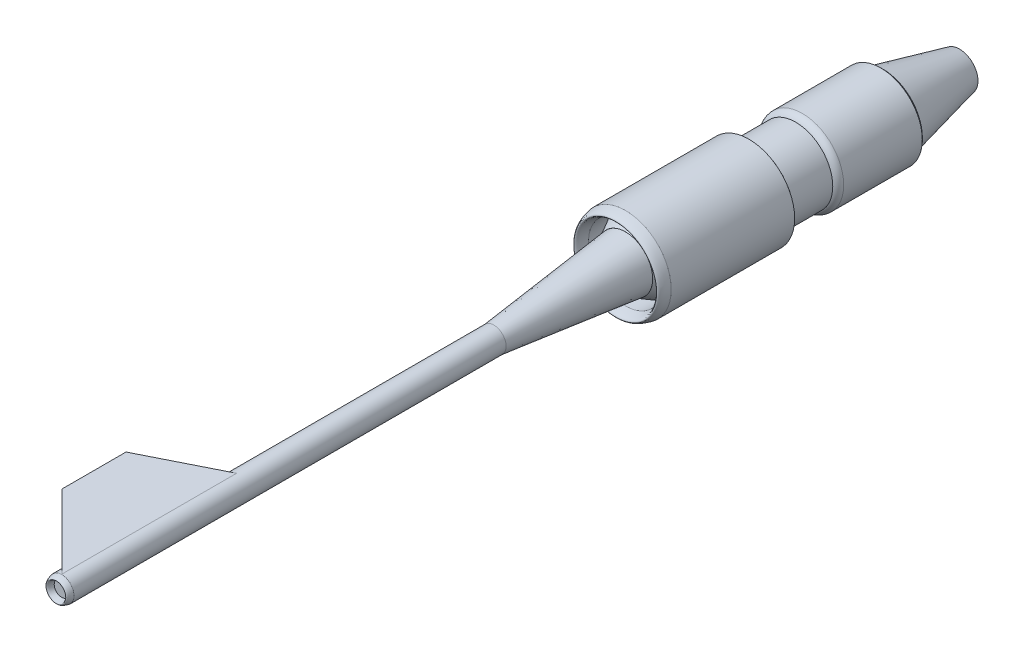
SolidWorks part; units mm, degrees
ref_plane "Front Plane" through (0, 0, 0) normal (0, 0, 1) x (1, 0, 0)
ref_plane "Top Plane" through (0, 0, 0) normal (0, 1, 0) x (1, 0, 0)
ref_plane "Right Plane" through (0, 0, 0) normal (1, 0, 0) x (0, 0, -1)
sketch "Sketch1" plane through (0, 0, 0) normal (0, 0, 1) x (1, 0, 0)
  circle A0 centre (0, 0) radius 416.25
  circle A1 centre (0, 0) radius 337.5
extrude "Boss-Extrude1" add sketch "Sketch1" against normal blind 1125
sketch "Sketch2" plane through (0, 0, 0) normal (1, 0, 0) x (0, 0, -1)
  line L0 (0, 416.25) -> (0, 337.5) construction
  line L1 (0, 337.5) -> (0, 376.875) construction
  line L2 (0, 376.875) -> (-90, 376.875) construction
  line L3 (0, 416.25) -> (0, 337.5)
  line L4 (0, 0) -> (98.8797, 0) construction
  spline S0 degree 2 poles (0, 337.5) (-180, 376.875) (0, 416.25) knots 0 0 0 1 1 1
revolve "Revolve1" add sketch "Sketch2" angle 360 about L4
ref_plane "Plane1" through (0, 0, 0) normal (0, 0, 1) x (1, 0, 0)
sketch "Sketch3" plane through (0, 0, 0) normal (0, 0, 1) x (1, 0, 0)
  circle A0 centre (0, 0) radius 247.5
sketch "Sketch4" plane through (0, 0, 0) normal (0, 1, 0) x (1, 0, 0)
  line L0 (0, 0) -> (0, -1200)
  line L1 (0, -1200) -> (112.5, -1200)
  line L2 (0, 0) -> (247.5, 0)
  line L3 (-247.5, 0) -> (247.5, 0) construction
  line L4 (-457.875, 0) -> (457.875, 0) construction
  line L5 (247.5, 0) -> (112.5, -1200)
revolve "Revolve2" add sketch "Sketch4" angle 360 about L0
sketch "Sketch5" plane through (0, 0, 1200) normal (0, 0, 1) x (1, 0, 0)
  circle A0 centre (0, 0) radius 112.5
extrude "Boss-Extrude2" add sketch "Sketch5" along normal blind 3937.5
sketch "Sketch14" plane through (0, 0, 0) normal (1, 0, 0) x (0, 0, -1)
  line L0 (-5137.5, 112.5) -> (-5137.5, 67.5)
  line L1 (-5137.5, 112.5) -> (-5137.5, -112.5) construction
  line L2 (-5137.5, 67.5) -> (-5137.5, 90)
  line L3 (-5137.5, 90) -> (-5187.5, 90) construction
  line L4 (-5137.5, 0) -> (-5198.2274, 0) construction
  line L5 (-5137.5, 112.5) -> (-5137.5, -112.5) construction
  spline S0 degree 2 poles (-5137.5, 67.5) (-5237.5, 90) (-5137.5, 112.5) knots 0 0 0 1 1 1
  dimension "D1" = 50
  dimension "D2" = 67.5
  dimension "D3" = 90
revolve "Revolve4" add sketch "Sketch14" angle 360 about L4
sketch "Sketch15" plane through (0, 0, -1125) normal (0, 0, -1) x (-1, 0, 0)
  circle A0 centre (0, 0) radius 337.5
extrude "Boss-Extrude5" add sketch "Sketch15" along normal blind 486 separate body
sketch "Sketch16" plane through (0, 0, -1611) normal (0, 0, -1) x (-1, 0, 0)
  line L0 (0, 337.5) -> (0, 416.25) construction
  line L1 (0, 376.875) -> (79.8334, 376.875) construction
  circle A0 centre (0, 0) radius 337.5 construction
  circle A1 centre (0, 0) radius 337.5 construction
  circle A2 centre (0, 0) radius 416.25 construction
  circle A4 centre (0, 0) radius 376.875
extrude "Boss-Extrude6" add sketch "Sketch16" along normal blind 716
sketch "Sketch17" plane through (0, 0, 0) normal (1, 0, 0) x (0, 0, -1)
  line L0 (2327, 0) -> (3043, 0)
  line L1 (2327, -376.875) -> (2327, 376.875) construction
  line L2 (3043, 0) -> (3043, 168.75)
  line L3 (1611, 337.5) -> (2327, 337.5) construction
  line L4 (2327, 0) -> (2327, 337.5)
  line L5 (2327, 337.5) -> (3043, 168.75)
revolve "Revolve5" add sketch "Sketch17" angle 360 about L0
sketch "Sketch18" plane through (0, 0, 0) normal (1, 0, 0) x (0, 0, -1)
  line L0 (0, 247.5) -> (306.6324, 416.25)
  line L1 (1125, 416.25) -> (0, 416.25) construction
  line L2 (0, 247.5) -> (306.6324, 247.5)
  line L3 (306.6324, 247.5) -> (306.6324, 416.25)
  line L4 (0, 0) -> (306.6324, 0) construction
revolve "Revolve6" add sketch "Sketch18" angle 360 about L4
sketch "Sketch19" plane through (0, 0, 0) normal (1, 0, 0) x (0, 0, -1)
  line L1 (1611, 337.5) -> (1611, -337.5) construction
  line L2 (1611, 0) -> (1611, 337.5) construction
  line L3 (1611, 337.5) -> (1551, 337.5)
  line L4 (1611, 0) -> (1571, 0) construction
  line L5 (1611, 337.5) -> (1125, 337.5) construction
  line L6 (1611, 337.5) -> (1611, 376.875)
  line L7 (1611, 376.875) -> (1611, -376.875) construction
  arc A0 (1551, 337.5) -> (1611, 376.875) centre (1614.9642, 305.4325) cw
revolve "Revolve9" add sketch "Sketch19" angle 360 about L4
sketch "Sketch20" plane through (0, 0, 0) normal (1, 0, 0) x (0, 0, -1)
  line L0 (1125, 337.5) -> (1125, 416.25)
  line L1 (1125, 337.5) -> (1155, 337.5)
  line L2 (1551, 337.5) -> (1125, 337.5) construction
  line L3 (1125, 0) -> (1175, 0) construction
  line L4 (1125, -416.25) -> (1125, 416.25) construction
  conic Q0 (1155, 337.5) -> (1125, 416.25) control (1155, 382.5893) rho 0.44632
revolve "Revolve11" add sketch "Sketch20" angle 360 about L3
sketch "Sketch21" plane through (0, 0, 0) normal (1, 0, 0) x (0, 0, -1)
  line L0 (2327, 337.5) -> (2327, 376.875)
  line L1 (2327, 0) -> (2377, 0) construction
  line L2 (2327, -376.875) -> (2327, 376.875) construction
  line L3 (2327, 337.5) -> (2356.2, 330.618)
  line L4 (3043, 168.75) -> (2327, 337.5) construction
  conic Q0 (2327, 376.875) -> (2356.2, 330.618) control (2356.2, 357.1875) rho 0.453502
revolve "Revolve12" add sketch "Sketch21" angle 360 about L1
sketch3d "3DSketch1"
  line L0 (1.7689, 112.4861, 5137.5) -> (-673.2311, 112.4861, 5137.5) construction
  circle A0 centre (0, 0, 5137.5) radius 112.5 construction
  point P2 (0, 0, 5250)
ref_plane "Plane2" through (0, 112.4861, 0) normal (0, 1, 0) x (1, 0, 0)
sketch "Sketch22" plane through (0, 112.4861, 0) normal (0, 1, 0) x (1, 0, 0)
  line L0 (1.7689, -5137.5) -> (1.7689, -3540)
  line L1 (-673.2311, -5137.5) -> (-673.2311, -4462.5) construction
  line L2 (-673.2311, -4462.5) -> (1.7689, -4462.5) construction
  line L3 (-673.2311, -4462.5) -> (1.7689, -5137.5)
  line L4 (-673.2311, -4462.5) -> (-673.2311, -3877.5)
  line L5 (-673.2311, -3877.5) -> (1.7689, -3540)
extrude "Boss-Extrude7" add sketch "Sketch22" against normal blind 50
sketch3d "3DSketch3"
  line L0 (0, 0, 0) -> (416.25, 0, 0)
  line L1 (416.25, 0, 0) -> (416.25, 0, -1125)
  line L2 (0, 0, 0) -> (409.9262, -72.2811, 0)
  line L3 (409.9262, -72.2811, 0) -> (416.438, -35.3508, 0)
  line L4 (409.9262, -72.2811, 0) -> (403.4144, -109.2113, 0)
  line L5 (0, 0, 0) -> (-416.25, 0, 0)
  line L6 (-416.25, 0, 0) -> (-416.25, -37.5, 0)
  line L7 (-416.25, 0, 0) -> (-416.25, 37.5, 0)
  circle A0 centre (0, 0, 0) radius 416.25 construction
  arc A1 (416.25, 0, 0) -> (409.9262, -72.2811, 0) centre (0, 0, 0) cw
  circle A2 centre (0, 0, -1125) radius 416.25 construction
  point P5 (0, 0, 416.25)
  point P9 (0, 0, -708.75)
  point P11 (0, 0, -416.25)
  dimension "D1" = 180
  dimension "D2" = 90
